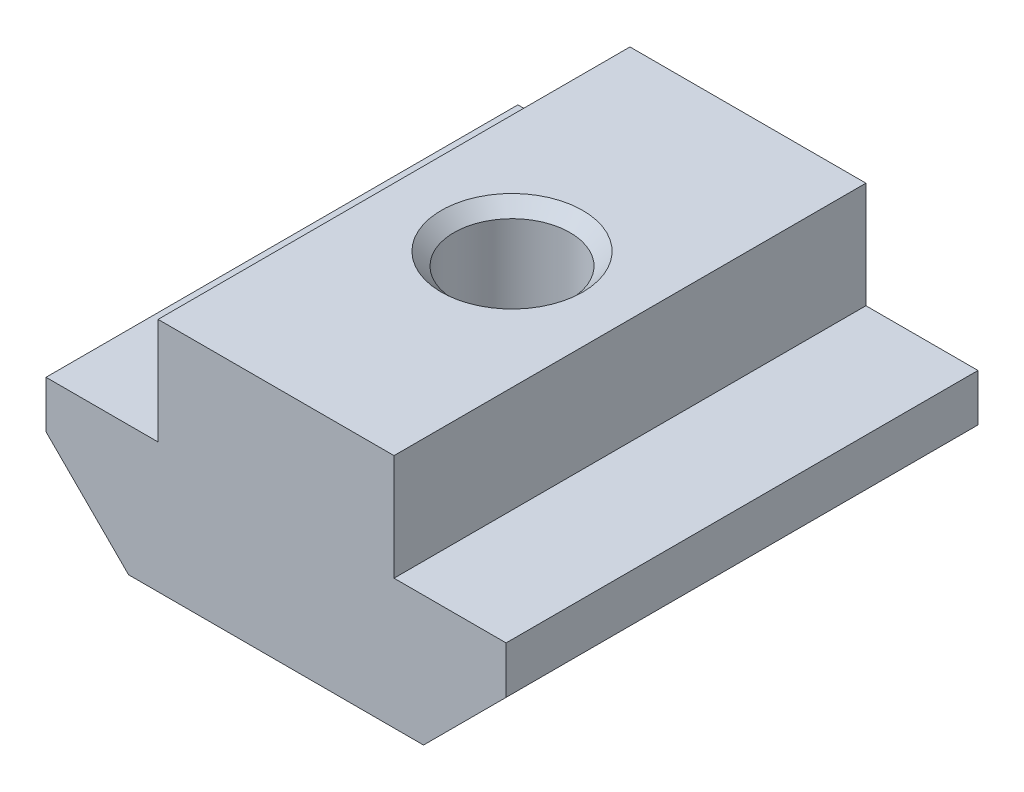
SolidWorks part; units mm, degrees
ref_plane "Plan de face" through (0, 0, 0) normal (0, 0, 1) x (1, 0, 0)
ref_plane "Plan de dessus" through (0, 0, 0) normal (0, 1, 0) x (1, 0, 0)
ref_plane "Plan de droite" through (0, 0, 0) normal (1, 0, 0) x (0, 0, -1)
ref_plane "Plan1" through (0, 0, -10) normal (0, 0, -1) x (-1, 0, 0)
sketch "Esquisse1" plane through (0, 0, -10) normal (0, 0, -1) x (-1, 0, 0)
  line L0 (9.75, -1.5) -> (9.75, 5)
  line L1 (9.75, 5) -> (-9.75, 5)
  line L2 (-9.75, 5) -> (-9.75, -1.5)
  line L3 (-9.75, -1.5) -> (-6.25, -5)
  line L4 (-6.25, -5) -> (6.25, -5)
  line L5 (6.25, -5) -> (9.75, -1.5)
extrude "Boss.-Extru.1" add sketch "Esquisse1" against normal blind 20
sketch "Esquisse2" plane through (0, 0, -10) normal (0, 0, -1) x (-1, 0, 0)
  line L0 (-9.75, 5) -> (-9.75, 0.5)
  line L1 (-9.75, 0.5) -> (-5, 0.5)
  line L2 (-5, 0.5) -> (-5, 5)
  line L3 (-5, 5) -> (-9.75, 5)
extrude "Enlèv. mat.-Extru.1" cut sketch "Esquisse2" against normal through all
sketch "Esquisse3" plane through (0, 0, -10) normal (0, 0, -1) x (-1, 0, 0)
  line L0 (9.75, 5) -> (5, 5)
  line L1 (5, 5) -> (5, 0.5)
  line L2 (5, 0.5) -> (9.75, 0.5)
  line L3 (9.75, 0.5) -> (9.75, 5)
extrude "Enlèv. mat.-Extru.2" cut sketch "Esquisse3" against normal through all
sketch "Esquisse4" plane through (0, 0, 0) normal (0, 0, 1) x (1, 0, 0)
  line L0 (3, 5) -> (0, 5)
  line L1 (0, 5) -> (0, -5)
  line L2 (0, -5) -> (3, -5)
  line L3 (3, -5) -> (2.4585, -4.4585)
  line L4 (2.4585, -4.4585) -> (2.4585, 4.4585)
  line L5 (2.4585, 4.4585) -> (3, 5)
  line L6 (0, 5) -> (0, -5) construction
revolve "Enlèvement de matière-Révolution1" cut sketch "Esquisse4" angle 360 about L6
